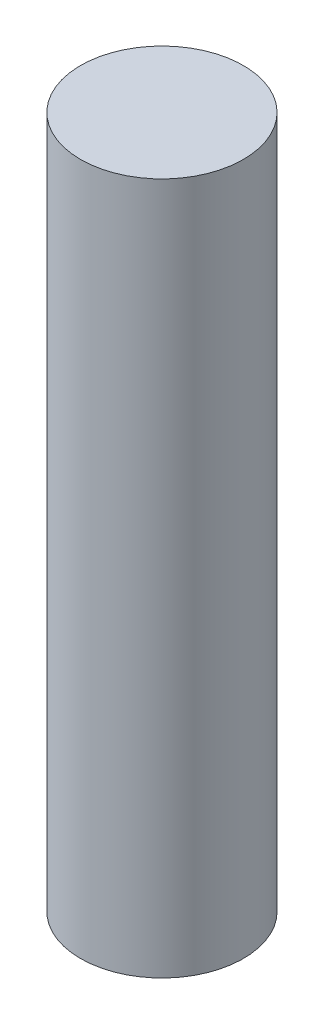
SolidWorks part; units mm, degrees
material "Cast Alloy Steel"
ref_plane "Front Plane" through (0, 0, 0) normal (0, 0, 1) x (1, 0, 0)
ref_plane "Top Plane" through (0, 0, 0) normal (0, 1, 0) x (1, 0, 0)
ref_plane "Right Plane" through (0, 0, 0) normal (1, 0, 0) x (0, 0, -1)
sketch "Sketch1" plane through (0, 0, 0) normal (0, 1, 0) x (1, 0, 0)
  circle A0 centre (0, 0) radius 20
  dimension "D1" = 40
extrude "Boss-Extrude1" add sketch "Sketch1" along normal blind 170 contours A0
